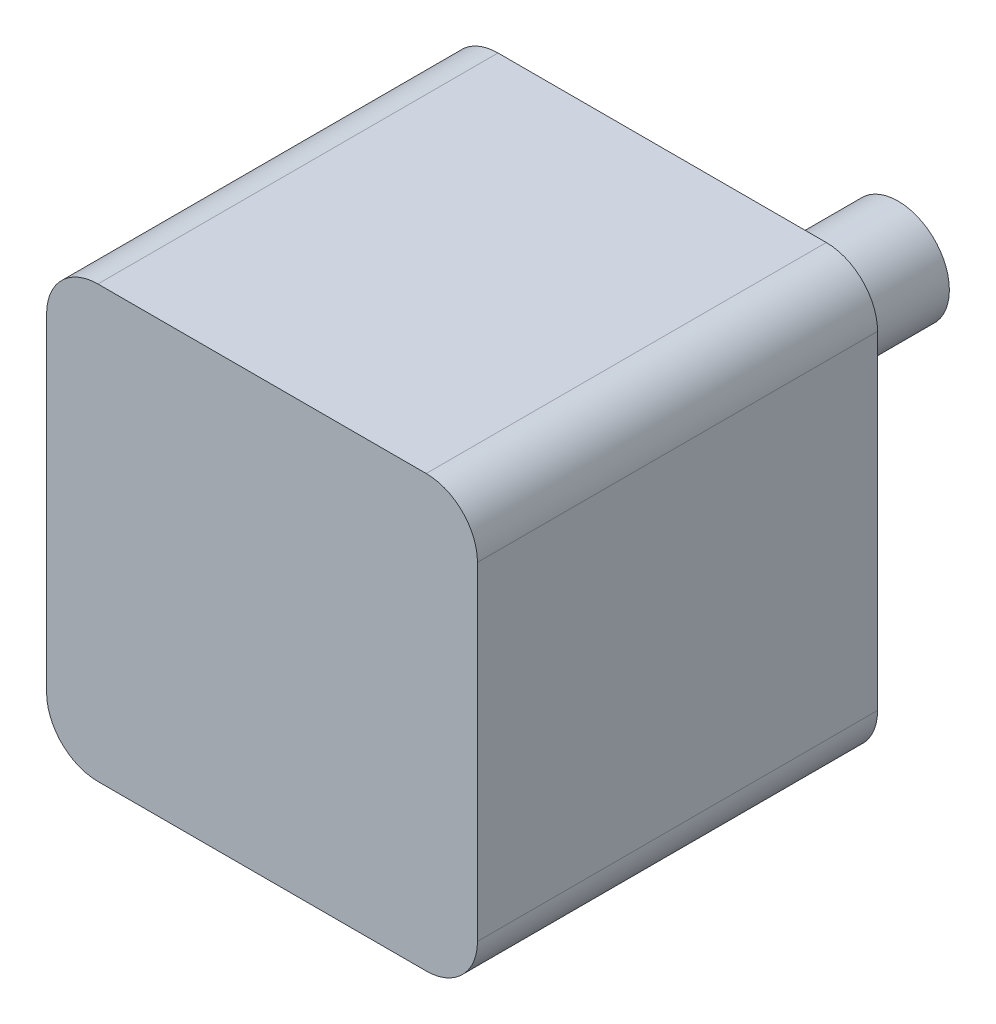
SolidWorks part; units mm, degrees
ref_plane "Plan de face" through (0, 0, 0) normal (0, 0, 1) x (1, 0, 0)
ref_plane "Plan de dessus" through (0, 0, 0) normal (0, 1, 0) x (1, 0, 0)
ref_plane "Plan de droite" through (0, 0, 0) normal (1, 0, 0) x (0, 0, -1)
sketch "Esquisse1" plane through (0, 0, 0) normal (0, 0, 1) x (1, 0, 0)
  line L1 (0, 0) -> (42, 0)
  line L2 (0, 0) -> (0, -42)
  line L3 (0, -42) -> (42, -42)
  line L4 (42, 0) -> (42, -42)
  dimension "D1" = 42
  dimension "D2" = 42
extrude "Boss.-Extru.1" add sketch "Esquisse1" along normal blind 39
fillet "Congé1" radius 5 4 edges at (42, -42, 19.5) (0, -42, 19.5) (0, 0, 19.5) (42, 0, 19.5)
sketch "Esquisse2" plane through (0, 0, 0) normal (0, 0, -1) x (-1, 0, 0)
  line L0 (0, 0) -> (0, -44.9052) construction
  line L1 (0, -44.9052) -> (-40.5355, -1.4645) construction
  line L2 (-40.5355, -1.4645) -> (-1.4645, -1.4645) construction
  line L3 (-1.4645, -1.4645) -> (-1.4645, -40.5355) construction
  line L4 (-1.4645, -40.5355) -> (-40.5355, -40.5355) construction
  line L5 (-40.5355, -40.5355) -> (-1.4645, -1.4645) construction
  line L6 (-1.4645, -1.4645) -> (-21, -21) construction
  line L7 (-21, -21) -> (-1.4645, -40.5355) construction
  arc A0 (-37, 0) -> (-42, -5) centre (-37, -5) ccw construction
  arc A1 (0, -5) -> (-5, 0) centre (-5, -5) ccw construction
  arc A2 (-5, -42) -> (0, -37) centre (-5, -37) ccw construction
  arc A3 (-42, -37) -> (-37, -42) centre (-37, -37) ccw construction
  circle A4 centre (-21, -21) radius 5
extrude "Boss.-Extru.2" add sketch "Esquisse2" along normal blind 23
